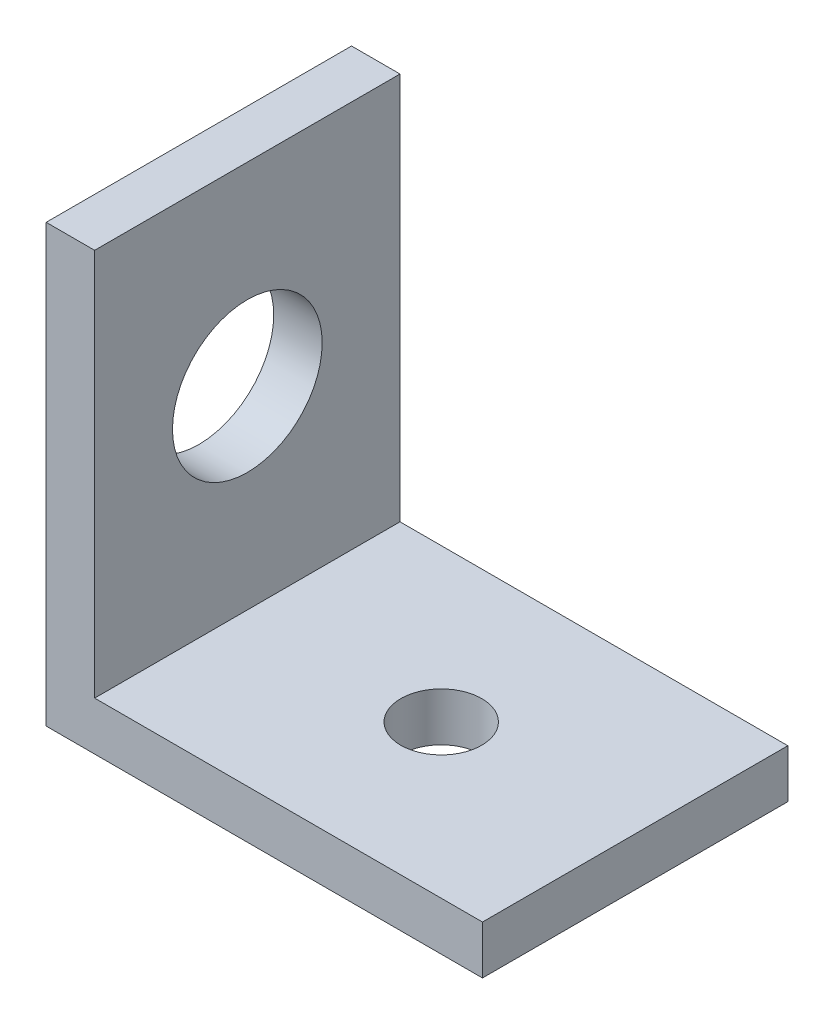
SolidWorks part; units mm, degrees
material "6063-T5"
ref_plane "Front Plane" through (0, 0, 0) normal (0, 0, 1) x (1, 0, 0)
ref_plane "Top Plane" through (0, 0, 0) normal (0, 1, 0) x (1, 0, 0)
ref_plane "Right Plane" through (0, 0, 0) normal (1, 0, 0) x (0, 0, -1)
sketch "Sketch1" plane through (0, 0, 0) normal (0, 0, 1) x (1, 0, 0)
  line L0 (0, 2.54) -> (0, 25.4)
  line L1 (0, 25.4) -> (-3.175, 25.4)
  line L2 (-3.175, 25.4) -> (-3.175, -3.175)
  line L3 (-3.175, -3.175) -> (25.4, -3.175)
  line L4 (25.4, -3.175) -> (25.4, 0)
  line L5 (25.4, 0) -> (2.54, 0)
  line L6 (0, 2.54) -> (0, 0)
  line L7 (0, 0) -> (2.54, 0)
  point P9 (0, 0)
  dimension "D1" = 3.175
  dimension "D2" = 28.575
  dimension "D3" = 28.575
extrude "Boss-Extrude1" add sketch "Sketch1" along normal blind 20 contours L0 L1 L2 L3 L4 L5 L7 L6
sketch "Sketch2" plane through (-3.175, 0, 0) normal (-1, 0, 0) x (0, 0, 1)
  line L0 (10, -3.175) -> (10, 12.7) construction
  line L1 (20, -3.175) -> (0, -3.175) construction
  circle A0 centre (10, 12.7) radius 1
  circle A1 centre (10, 12.7) radius 9.525
  dimension "D2" = 2
  dimension "D3" = 19.05
  dimension "D1" = 15.875
sketch "Sketch3" plane through (0, 0, 0) normal (0, 1, 0) x (1, 0, 0)
  line L0 (0, -20) -> (25.4, 0) construction
  line L1 (25.4, 0) -> (0, 0) construction
  line L2 (0, 0) -> (25.4, -20) construction
  line L3 (0, -20) -> (0, 0) construction
  line L4 (0, -20) -> (25.4, -20) construction
  circle A0 centre (12.7, -10) radius 2.5
  point P10 (2.54, -20)
  point P11 (0, 0)
  point P12 (0, -19.7956)
  point P15 (0, 0)
  point P17 (0, -20)
  dimension "D1" = 5
hole_wizard "3/8 Clearance Hole1" positions "Sketch4" profile "Sketch5" hole size "3/8" standard "ANSI Inch" end condition through all
sketch "Sketch4" plane through (-3.175, 0, 0) normal (-1, 0, 0) x (0, 0, 1)
  point P0 (10, 12.7)
sketch "Sketch5" plane through (-3.175, 12.7, 10) normal (0, 1, 0) x (0, 0, 1)
  line L0 (0, 0) -> (0, 28.575)
  line L1 (0, 28.575) -> (4.9022, 28.575)
  line L2 (4.9022, 28.575) -> (4.9022, 0)
  line L5 (4.9022, 0) -> (0, 0)
  line L11 (0, -6.35) -> (0, 107.95) construction
  dimension "Thru Hole Dia." = 9.8044
  dimension "Thru Hole Depth" = 28.575
hole_wizard "M5 Clearance Hole1" positions "Sketch6" profile "Sketch7" hole size "M5" standard "ANSI Metric" end condition through all
sketch "Sketch6" plane through (0, 0, 0) normal (0, 1, 0) x (1, 0, 0)
  point P0 (12.7, -10)
sketch "Sketch7" plane through (12.7, 0, 10) normal (1, 0, 0) x (0, 0, 1)
  line L0 (0, 0) -> (0, 3.175)
  line L1 (0, 3.175) -> (2.65, 3.175)
  line L2 (2.65, 3.175) -> (2.65, 0)
  line L5 (2.65, 0) -> (0, 0)
  line L11 (0, -6.35) -> (0, 107.95) construction
  dimension "Thru Hole Dia." = 5.3
  dimension "Thru Hole Depth" = 3.175
extrude "Cut-Extrude1" cut sketch "Sketch2" against normal blind 0.001 contours A1
